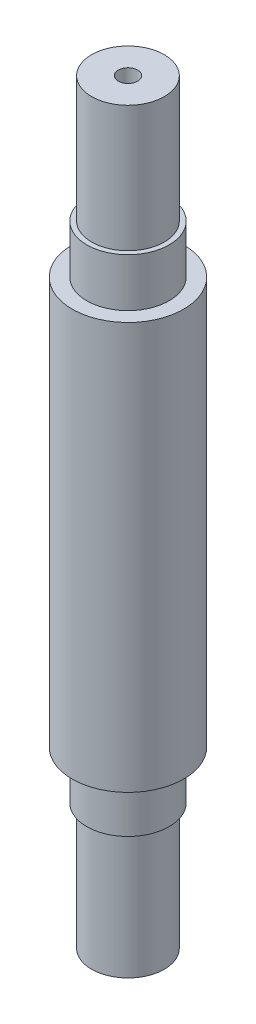
SolidWorks part; units mm, degrees
material "AISI 1045 Steel, cold drawn"
ref_plane "Front Plane" through (0, 0, 0) normal (0, 0, 1) x (1, 0, 0)
ref_plane "Top Plane" through (0, 0, 0) normal (0, 1, 0) x (1, 0, 0)
ref_plane "Right Plane" through (0, 0, 0) normal (1, 0, 0) x (0, 0, -1)
sketch "Sketch1" plane through (0, 0, 0) normal (0, 0, 1) x (1, 0, 0)
  line L0 (0, 28.462) -> (0, -34.7363) construction
  line L1 (1, 32.462) -> (3.75, 32.462)
  line L2 (4.25, 19.462) -> (4.25, 14.462)
  line L3 (4.25, 14.462) -> (5.75, 14.462)
  line L4 (5.75, 14.462) -> (5.75, -27.538)
  line L5 (5.75, -27.538) -> (4.25, -27.538)
  line L6 (4.25, -27.538) -> (4.25, -32.538)
  line L7 (3.75, -45.538) -> (1, -45.538)
  line L8 (0, -41.7048) -> (0, 28.462) construction
  line L9 (4.25, 19.462) -> (3.75, 19.462)
  line L10 (3.75, 19.462) -> (3.75, 32.462)
  line L11 (4.25, -32.538) -> (3.75, -32.538)
  line L12 (3.75, -32.538) -> (3.75, -45.538)
  line L13 (0, 28.462) -> (0, -41.7048)
  line L14 (1, -42.538) -> (0, -41.7048)
  line L18 (1, 32.462) -> (1, 29.462)
  line L20 (1, -45.538) -> (1, -42.538)
  line L23 (1, 29.462) -> (0, 28.462)
  dimension "D1" = 5
  dimension "D2" = 13
  dimension "D3" = 42
  dimension "D4" = 11.5
  dimension "D5" = 1.5
  dimension "D6" = 0.5
revolve "Revolve1" add sketch "Sketch1" angle 360 about L0
